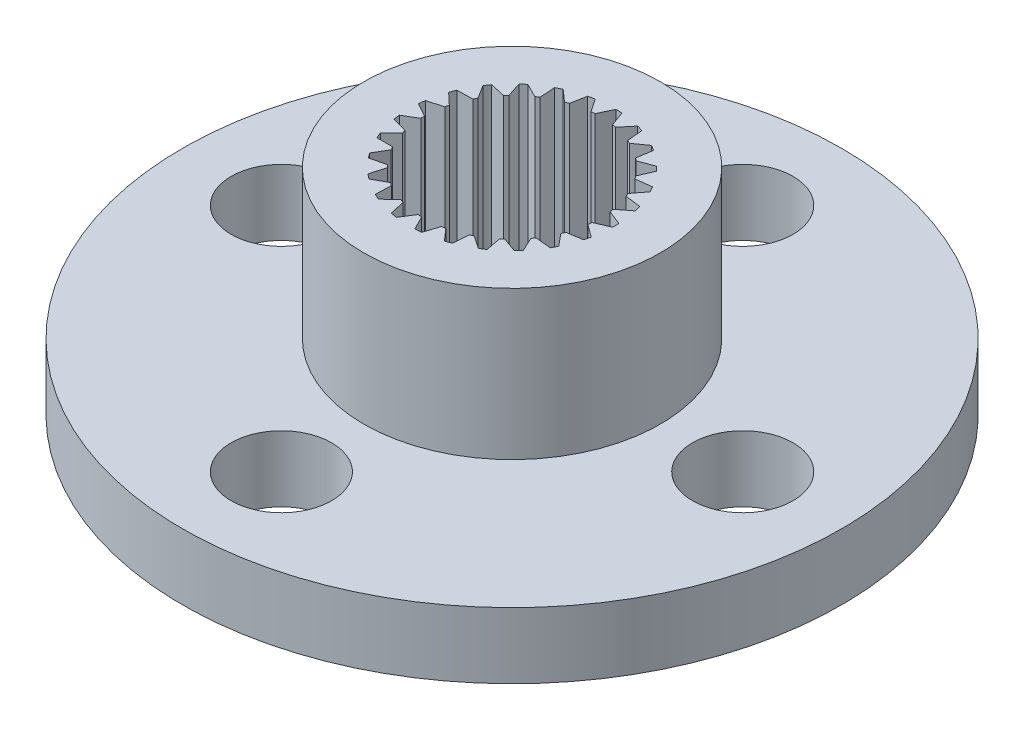
SolidWorks part; units mm, degrees
ref_plane "Front Plane" through (0, 0, 0) normal (0, 0, 1) x (1, 0, 0)
ref_plane "Top Plane" through (0, 0, 0) normal (0, 1, 0) x (1, 0, 0)
ref_plane "Right Plane" through (0, 0, 0) normal (1, 0, 0) x (0, 0, -1)
sketch "Sketch1" plane through (24.3015, 0, -59.2505) normal (0, -1, 0) x (0.9556, 0, 0.2946)
  line L0 (-1.3378, 2.3147) -> (-1.7435, 2.5633)
  line L1 (-1.8991, 2.4502) -> (-1.788, 1.9876)
  line L2 (-1.8714, 1.9093) -> (-2.3261, 2.0492)
  line L3 (-2.4487, 1.901) -> (-2.2261, 1.4805)
  line L4 (-2.2874, 1.3839) -> (-2.7627, 1.4063)
  line L5 (-2.8446, 1.2323) -> (-2.5244, 0.8804)
  line L6 (-2.5597, 0.7715) -> (-3.0256, 0.6751)
  line L7 (-3.0616, 0.4861) -> (-2.664, 0.2249)
  line L8 (-2.6712, 0.1107) -> (-3.0984, -0.0986)
  line L9 (-3.0864, -0.2905) -> (-2.6362, -0.4446)
  line L10 (-2.6148, -0.5571) -> (-2.9766, -0.866)
  line L11 (-2.9171, -1.0489) -> (-2.4428, -1.0863)
  line L12 (-2.3941, -1.1898) -> (-2.6677, -1.5791)
  line L13 (-2.5646, -1.7415) -> (-2.0959, -1.6597)
  line L14 (-2.023, -1.7478) -> (-2.1912, -2.1929)
  line L15 (-2.051, -2.3245) -> (-1.6174, -2.1288)
  line L16 (-1.5248, -2.196) -> (-1.577, -2.6689)
  line L17 (-1.4085, -2.7616) -> (-1.0371, -2.4641)
  line L18 (-0.9307, -2.5062) -> (-0.8637, -2.9772)
  line L19 (-0.6774, -3.0251) -> (-0.3918, -2.6446)
  line L20 (-0.2782, -2.659) -> (-0.0962, -3.0985)
  line L21 (0.0962, -3.0985) -> (0.2782, -2.659)
  line L22 (0.3918, -2.6446) -> (0.6774, -3.0251)
  line L23 (0.8637, -2.9772) -> (0.9307, -2.5062)
  line L24 (1.0371, -2.4641) -> (1.4085, -2.7616)
  line L25 (1.577, -2.6689) -> (1.5248, -2.196)
  line L26 (1.6174, -2.1288) -> (2.051, -2.3245)
  line L27 (2.1912, -2.1929) -> (2.023, -1.7478)
  line L28 (2.0959, -1.6597) -> (2.5646, -1.7415)
  line L29 (2.6677, -1.5791) -> (2.3941, -1.1898)
  line L30 (2.4428, -1.0863) -> (2.9171, -1.0489)
  line L31 (2.9766, -0.866) -> (2.6148, -0.5571)
  line L32 (2.6362, -0.4446) -> (3.0864, -0.2905)
  line L33 (3.0984, -0.0986) -> (2.6712, 0.1107)
  line L34 (2.664, 0.2249) -> (3.0616, 0.4861)
  line L35 (3.0256, 0.6751) -> (2.5597, 0.7715)
  line L36 (2.5244, 0.8804) -> (2.8446, 1.2323)
  line L37 (2.7627, 1.4063) -> (2.2874, 1.3839)
  line L38 (2.2261, 1.4805) -> (2.4487, 1.901)
  line L39 (2.3261, 2.0492) -> (1.8714, 1.9093)
  line L40 (1.788, 1.9876) -> (1.8991, 2.4502)
  line L41 (1.7435, 2.5633) -> (1.3378, 2.3147)
  line L42 (1.2375, 2.3698) -> (1.23, 2.8455)
  line L43 (1.0512, 2.9163) -> (0.7201, 2.5747)
  line L44 (0.6093, 2.6031) -> (0.4837, 3.062)
  line L45 (0.2929, 3.0861) -> (0.0572, 2.6729)
  line L46 (-0.0572, 2.6729) -> (-0.2929, 3.0861)
  line L47 (-0.4837, 3.062) -> (-0.6093, 2.6031)
  line L48 (-0.7201, 2.5747) -> (-1.0512, 2.9163)
  line L49 (-1.23, 2.8455) -> (-1.2375, 2.3698)
  line L200 (-1.8428, 2.4303) -> (-1.7394, 1.9993) construction
  line L201 (-1.3639, 2.272) -> (-1.7419, 2.5037) construction
  line L202 (-1.8861, 1.8615) -> (-2.3098, 1.9918) construction
  line L203 (-2.3893, 1.8957) -> (-2.1819, 1.5039) construction
  line L204 (-2.2898, 1.3339) -> (-2.7326, 1.3548) construction
  line L205 (-2.7857, 1.2419) -> (-2.4874, 0.914) construction
  line L206 (-3.007, 0.5101) -> (-2.6365, 0.2667) construction
  line L207 (-2.5496, 0.7226) -> (-2.9837, 0.6327) construction
  line L208 (-3.0394, -0.2537) -> (-2.62, -0.3973) construction
  line L209 (-2.6492, 0.0658) -> (-3.0473, -0.1292) construction
  line L210 (-2.8808, -1.0016) -> (-2.4389, -1.0364) construction
  line L211 (-2.5823, -0.5951) -> (-2.9194, -0.883) construction
  line L212 (-2.5412, -1.6866) -> (-2.1045, -1.6104) construction
  line L213 (-2.3532, -1.2186) -> (-2.6081, -1.5812) construction
  line L214 (-2.0419, -2.2656) -> (-1.6379, -2.0832) construction
  line L215 (-1.9762, -1.7655) -> (-2.1329, -2.1802) construction
  line L216 (-1.4144, -2.7022) -> (-1.0684, -2.4251) construction
  line L217 (-1.4751, -2.2015) -> (-1.5237, -2.6421) construction
  line L218 (-0.6979, -2.9691) -> (-0.4318, -2.6146) construction
  line L219 (-0.8812, -2.4992) -> (-0.8188, -2.938) construction
  line L220 (0.0624, -3.0494) -> (0.232, -2.6398) construction
  line L221 (-0.232, -2.6398) -> (-0.0624, -3.0494) construction
  line L222 (0.8188, -2.938) -> (0.8812, -2.4992) construction
  line L223 (0.4318, -2.6146) -> (0.6979, -2.9691) construction
  line L224 (1.0684, -2.4251) -> (1.4144, -2.7022) construction
  line L225 (1.5237, -2.6421) -> (1.4751, -2.2015) construction
  line L226 (1.6379, -2.0832) -> (2.0419, -2.2656) construction
  line L227 (2.1329, -2.1802) -> (1.9762, -1.7655) construction
  line L228 (2.1045, -1.6104) -> (2.5412, -1.6866) construction
  line L229 (2.6081, -1.5812) -> (2.3532, -1.2186) construction
  line L230 (2.4389, -1.0364) -> (2.8808, -1.0016) construction
  line L231 (2.9194, -0.883) -> (2.5823, -0.5951) construction
  line L232 (3.0473, -0.1292) -> (2.6492, 0.0658) construction
  line L233 (2.62, -0.3973) -> (3.0394, -0.2537) construction
  line L234 (2.9837, 0.6327) -> (2.5496, 0.7226) construction
  line L235 (2.6365, 0.2667) -> (3.007, 0.5101) construction
  line L236 (2.7326, 1.3548) -> (2.2898, 1.3339) construction
  line L237 (2.4874, 0.914) -> (2.7857, 1.2419) construction
  line L238 (2.3098, 1.9918) -> (1.8861, 1.8615) construction
  line L239 (2.1819, 1.5039) -> (2.3893, 1.8957) construction
  line L240 (1.7394, 1.9993) -> (1.8428, 2.4303) construction
  line L241 (1.7419, 2.5037) -> (1.3639, 2.272) construction
  line L242 (1.0645, 2.8582) -> (0.756, 2.5399) construction
  line L243 (1.1875, 2.369) -> (1.1806, 2.8123) construction
  line L244 (0.5611, 2.5899) -> (0.4441, 3.0175) construction
  line L245 (0.3203, 3.0331) -> (0.1007, 2.6481) construction
  line L246 (-0.4441, 3.0175) -> (-0.5611, 2.5899) construction
  line L247 (-0.1007, 2.6481) -> (-0.3203, 3.0331) construction
  line L248 (-1.1806, 2.8123) -> (-1.1875, 2.369) construction
  line L249 (-0.756, 2.5399) -> (-1.0645, 2.8582) construction
  arc A0 (-1.7435, 2.5633) -> (-1.8991, 2.4502) centre (0, 0) ccw
  arc A1 (-2.3261, 2.0492) -> (-2.4487, 1.901) centre (0, 0) ccw
  arc A2 (-2.7627, 1.4063) -> (-2.8446, 1.2323) centre (0, 0) ccw
  arc A3 (-3.0256, 0.6751) -> (-3.0616, 0.4861) centre (0, 0) ccw
  arc A4 (-3.0984, -0.0986) -> (-3.0864, -0.2905) centre (0, 0) ccw
  arc A5 (-2.9766, -0.866) -> (-2.9171, -1.0489) centre (0, 0) ccw
  arc A6 (-2.6677, -1.5791) -> (-2.5646, -1.7415) centre (0, 0) ccw
  arc A7 (-2.1912, -2.1929) -> (-2.051, -2.3245) centre (0, 0) ccw
  arc A8 (-1.577, -2.6689) -> (-1.4085, -2.7616) centre (0, 0) ccw
  arc A9 (-0.8637, -2.9772) -> (-0.6774, -3.0251) centre (0, 0) ccw
  arc A10 (-0.0962, -3.0985) -> (0.0962, -3.0985) centre (0, 0) ccw
  arc A11 (0.6774, -3.0251) -> (0.8637, -2.9772) centre (0, 0) ccw
  arc A12 (1.4085, -2.7616) -> (1.577, -2.6689) centre (0, 0) ccw
  arc A13 (2.051, -2.3245) -> (2.1912, -2.1929) centre (0, 0) ccw
  arc A14 (2.5646, -1.7415) -> (2.6677, -1.5791) centre (0, 0) ccw
  arc A15 (2.9171, -1.0489) -> (2.9766, -0.866) centre (0, 0) ccw
  arc A16 (3.0864, -0.2905) -> (3.0984, -0.0986) centre (0, 0) ccw
  arc A17 (3.0616, 0.4861) -> (3.0256, 0.6751) centre (0, 0) ccw
  arc A18 (2.8446, 1.2323) -> (2.7627, 1.4063) centre (0, 0) ccw
  arc A19 (2.4487, 1.901) -> (2.3261, 2.0492) centre (0, 0) ccw
  arc A20 (1.8991, 2.4502) -> (1.7435, 2.5633) centre (0, 0) ccw
  arc A21 (1.23, 2.8455) -> (1.0512, 2.9163) centre (0, 0) ccw
  arc A22 (0.4837, 3.062) -> (0.2929, 3.0861) centre (0, 0) ccw
  arc A23 (-0.2929, 3.0861) -> (-0.4837, 3.062) centre (0, 0) ccw
  arc A24 (-1.0512, 2.9163) -> (-1.23, 2.8455) centre (0, 0) ccw
  circle A25 centre (0, 0) radius 2.6735
  circle A152 centre (0, 0) radius 4.5
  arc A205 (-1.7419, 2.5037) -> (-1.8428, 2.4303) centre (0, 0) ccw construction
  arc A206 (-2.3098, 1.9918) -> (-2.3893, 1.8957) centre (0, 0) ccw construction
  arc A208 (-2.7326, 1.3548) -> (-2.7857, 1.2419) centre (0, 0) ccw construction
  arc A211 (-2.9837, 0.6327) -> (-3.007, 0.5101) centre (0, 0) ccw construction
  arc A213 (-3.0473, -0.1292) -> (-3.0394, -0.2537) centre (0, 0) ccw construction
  arc A215 (-2.9194, -0.883) -> (-2.8808, -1.0016) centre (0, 0) ccw construction
  arc A217 (-2.6081, -1.5812) -> (-2.5412, -1.6866) centre (0, 0) ccw construction
  arc A219 (-2.1329, -2.1802) -> (-2.0419, -2.2656) centre (0, 0) ccw construction
  arc A221 (-1.5237, -2.6421) -> (-1.4144, -2.7022) centre (0, 0) ccw construction
  arc A223 (-0.8188, -2.938) -> (-0.6979, -2.9691) centre (0, 0) ccw construction
  arc A225 (-0.0624, -3.0494) -> (0.0624, -3.0494) centre (0, 0) ccw construction
  arc A227 (0.6979, -2.9691) -> (0.8188, -2.938) centre (0, 0) ccw construction
  arc A228 (1.4144, -2.7022) -> (1.5237, -2.6421) centre (0, 0) ccw construction
  arc A230 (2.0419, -2.2656) -> (2.1329, -2.1802) centre (0, 0) ccw construction
  arc A232 (2.5412, -1.6866) -> (2.6081, -1.5812) centre (0, 0) ccw construction
  arc A234 (2.8808, -1.0016) -> (2.9194, -0.883) centre (0, 0) ccw construction
  arc A237 (3.0394, -0.2537) -> (3.0473, -0.1292) centre (0, 0) ccw construction
  arc A239 (3.007, 0.5101) -> (2.9837, 0.6327) centre (0, 0) ccw construction
  arc A241 (2.7857, 1.2419) -> (2.7326, 1.3548) centre (0, 0) ccw construction
  arc A243 (2.3893, 1.8957) -> (2.3098, 1.9918) centre (0, 0) ccw construction
  arc A244 (1.8428, 2.4303) -> (1.7419, 2.5037) centre (0, 0) ccw construction
  arc A247 (1.1806, 2.8123) -> (1.0645, 2.8582) centre (0, 0) ccw construction
  arc A248 (0.4441, 3.0175) -> (0.3203, 3.0331) centre (0, 0) ccw construction
  arc A251 (-0.3203, 3.0331) -> (-0.4441, 3.0175) centre (0, 0) ccw construction
  arc A253 (-1.0645, 2.8582) -> (-1.1806, 2.8123) centre (0, 0) ccw construction
  dimension "D2" = 9
  dimension "D1" = 0.05
extrude "Boss-Extrude1" add sketch "Sketch1" against normal blind 6.5 contours A152 L43 A25 L44 A22 L45 L46 A23 L47 L48 A24 L49 L0 A0 L1 L2 A1 L3 L4 A2 L5 L6 A3 L7 L8 A4 L9 L10 A5 L11 L12 A6 L13 L14 A7 L15 L16 A8 L17
sketch "Sketch2" plane through (0, 0, 0) normal (0, -1, 0) x (-1, 0, 0)
  circle A0 centre (-24.3015, 59.2505) radius 10
  dimension "D1" = 20
extrude "Boss-Extrude2" add sketch "Sketch2" against normal blind 2
sketch "Sketch3" plane through (0, 0, 0) normal (0, -1, 0) x (-1, 0, 0)
  circle A6 centre (-24.3015, 66.2505) radius 1.525
  circle A8 centre (-17.3015, 59.2505) radius 1.525
  circle A9 centre (-24.3015, 52.2505) radius 1.525
  circle A10 centre (-31.3015, 59.2505) radius 1.525
  circle A13 centre (-24.3015, 59.2505) radius 10
  circle A14 centre (-24.3015, 59.2505) radius 10 construction
  point P17 (-24.3015, 59.2505)
  dimension "D1" = 3.05
  dimension "D4" = 14
  dimension "D2" = 4
  dimension "D3" = 0
extrude "Cut-Extrude1" cut sketch "Sketch3" against normal through all
